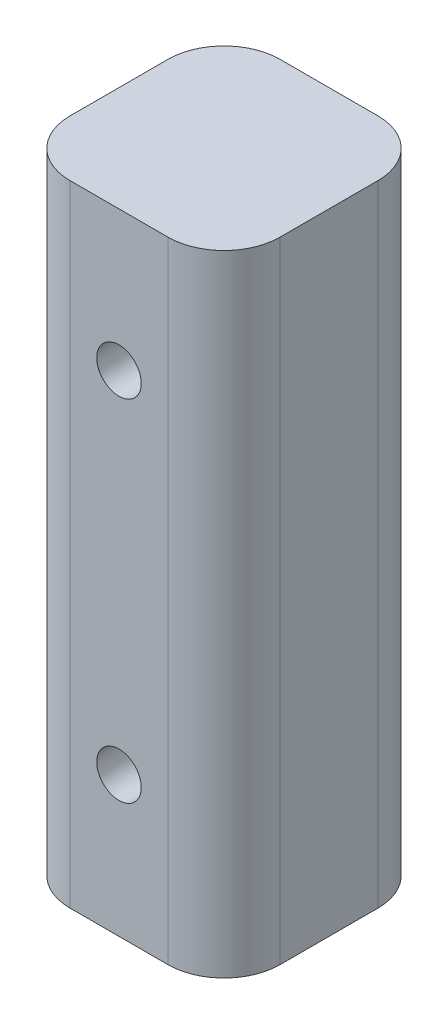
SolidWorks part; units mm, degrees
ref_plane "Front Plane" through (0, 0, 0) normal (0, 0, 1) x (1, 0, 0)
ref_plane "Top Plane" through (0, 0, 0) normal (0, 1, 0) x (1, 0, 0)
ref_plane "Right Plane" through (0, 0, 0) normal (1, 0, 0) x (0, 0, -1)
sketch "Sketch1" plane through (0, 0, 0) normal (0, 1, 0) x (1, 0, 0)
  line L1 (-4.445, 9.525) -> (4.445, 9.525)
  line L2 (-9.525, 4.445) -> (-9.525, -4.445)
  line L3 (-4.445, -9.525) -> (4.445, -9.525)
  line L4 (9.525, 4.445) -> (9.525, -4.445)
  line L5 (-9.525, 9.525) -> (9.525, -9.525) construction
  line L6 (-9.525, -9.525) -> (9.525, 9.525) construction
  arc A0 (-4.445, 9.525) -> (-9.525, 4.445) centre (-4.445, 4.445) ccw
  arc A1 (-9.525, -4.445) -> (-4.445, -9.525) centre (-4.445, -4.445) ccw
  arc A2 (4.445, -9.525) -> (9.525, -4.445) centre (4.445, -4.445) ccw
  arc A3 (9.525, 4.445) -> (4.445, 9.525) centre (4.445, 4.445) ccw
  point P0 (0, 0)
  dimension "D3" = 5.08
  dimension "D1" = 19.05
extrude "Boss-Extrude1" add sketch "Sketch1" along normal blind 57.15
hole_wizard "#10-32 Tapped Hole1" positions "Sketch2" profile "Sketch4" tap size "#10-32" standard "ANSI Inch" end condition through all
sketch "Sketch2" plane through (0, 0, 9.525) normal (0, 0, 1) x (1, 0, 0)
  line L5 (0, 57.15) -> (0, 44.45)
  line L6 (-4.445, 57.15) -> (4.445, 57.15) construction
  line L7 (0, 44.45) -> (0, 12.7)
  line L8 (0, 12.7) -> (0, 0)
  line L9 (-4.445, 0) -> (4.445, 0) construction
  point P0 (0, 44.45)
  point P2 (0, 12.7)
  dimension "D1" = 12.7
sketch "Sketch4" plane through (0, 44.45, 9.525) normal (1, 0, 0) x (0, -1, 0)
  line L0 (0, 0) -> (0, 19.05)
  line L1 (0, 19.05) -> (2.0193, 19.05)
  line L2 (2.0193, 19.05) -> (2.0193, 0)
  line L5 (2.0193, 0) -> (0, 0)
  line L11 (0, -6.35) -> (0, 107.95) construction
  dimension "Thru Tap Drill Dia." = 4.0386
  dimension "Thru Tap Drill Depth" = 19.05
cosmetic thread "Hole Thread1" parameters "D2"=4.826
cosmetic thread "Hole Thread2" parameters "D2"=4.826
